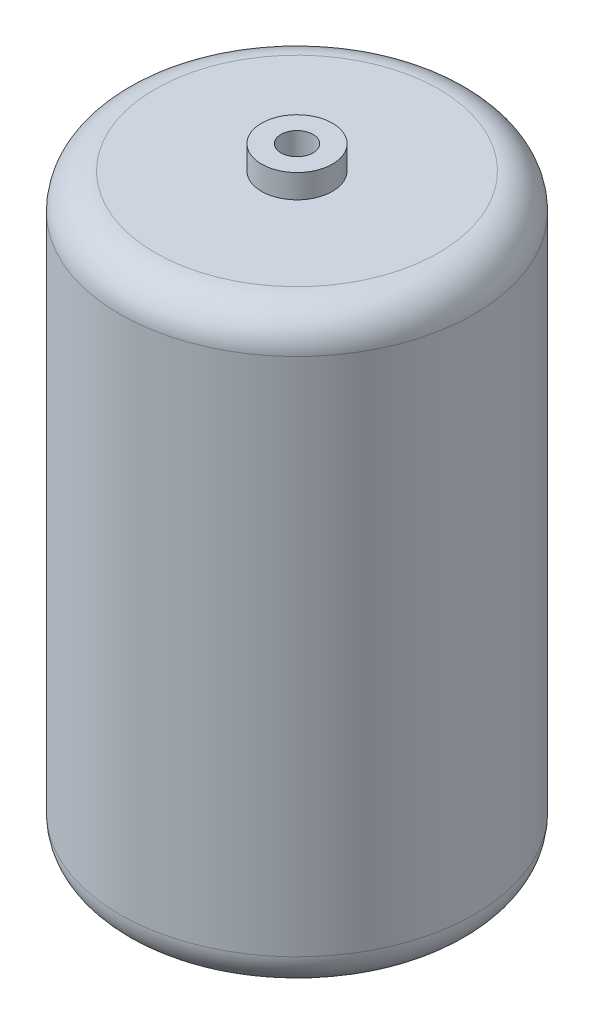
SolidWorks part; units mm, degrees
material "PP Homopolymer"
ref_plane "Front Plane" through (0, 0, 0) normal (0, 0, 1) x (1, 0, 0)
ref_plane "Top Plane" through (0, 0, 0) normal (0, 1, 0) x (1, 0, 0)
ref_plane "Right Plane" through (0, 0, 0) normal (1, 0, 0) x (0, 0, -1)
sketch "Sketch1" plane through (0, 0, 0) normal (0, 1, 0) x (1, 0, 0)
  circle A0 centre (0, 0) radius 19.05
  dimension "D1" = 38.1
extrude "Boss-Extrude1" add sketch "Sketch1" along normal blind 63.5
fillet "Fillet1" radius 3.81 2 edges at (0, 0, 19.05) (0, 63.5, 19.05)
sketch "Sketch2" plane through (0, 63.5, 0) normal (0, 1, 0) x (1, 0, 0)
  circle A0 centre (0, 0) radius 3.81
  dimension "D1" = 7.62
extrude "Boss-Extrude2" add sketch "Sketch2" along normal blind 2.54
sketch "Sketch3" plane through (0, 66.04, 0) normal (0, 1, 0) x (1, 0, 0)
  point P0 (0, 0)
hole_wizard "#8-32 Tapped Hole1" positions "Sketch3" profile "Sketch5" tap size "#8-32" standard "ANSI Inch"
sketch "Sketch5" plane through (0, 66.04, 0) normal (1, 0, 0) x (0, 0, 1)
  line L0 (0, 0) -> (0, 13.5752)
  line L1 (0, 13.5752) -> (1.7272, 12.5374)
  line L2 (1.7272, 12.5374) -> (1.7272, 0)
  line L5 (1.7272, 0) -> (0, 0)
  line L10 (0, 13.5752) -> (-1.7272, 12.5374) construction
  line L11 (0, -6.35) -> (0, 107.95) construction
  dimension "Tap Drill Dia." = 3.4544
  dimension "Tap Drill Depth" = 12.5374
  dimension "Drill Angle" = 118
cosmetic thread "Hole Thread1" parameters "D1"=10.16, "D2"=4.1656
sketch "Sketch6" plane through (0, 0, 0) normal (1, 0, 0) x (0, 0, -1)
  line L1 (0, 5.5127) -> (16.9073, 5.5127)
  line L2 (0, 5.5127) -> (0, 58.3372)
  line L3 (0, 58.3372) -> (16.9073, 58.3372)
  line L4 (16.9073, 5.5127) -> (16.9073, 58.3372)
revolve "Cut-Revolve1" cut sketch "Sketch6" angle 360 about L2
